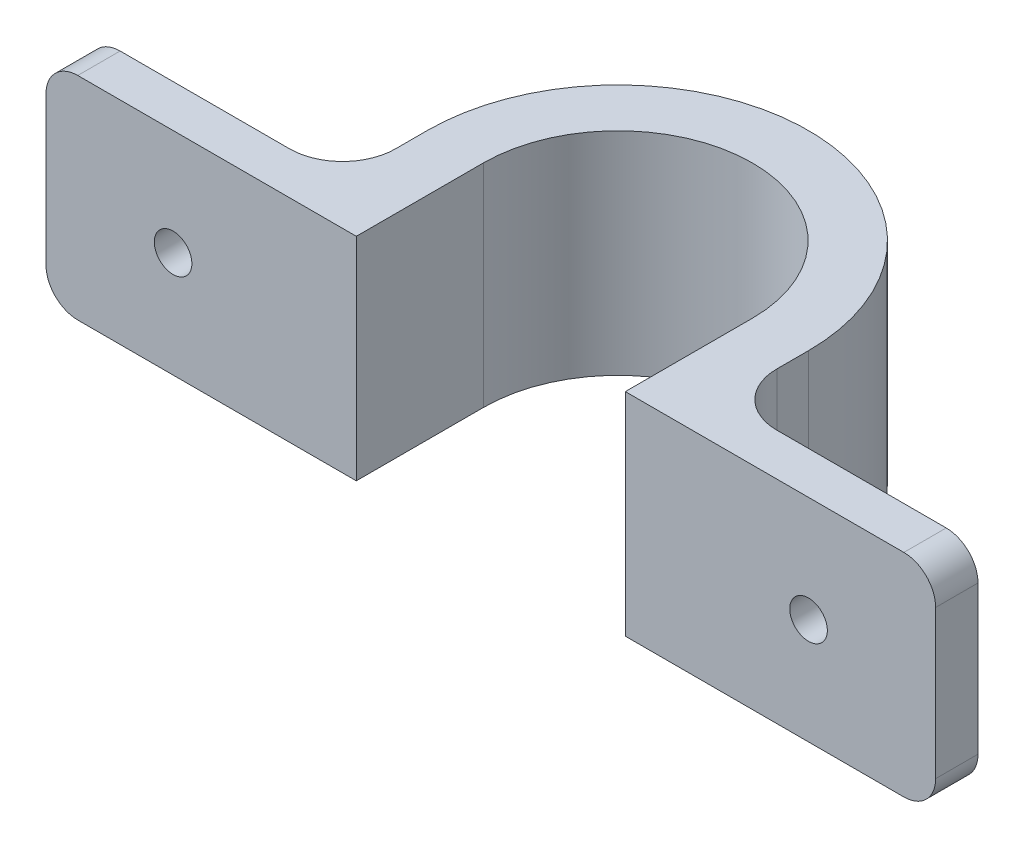
SolidWorks part; units mm, degrees
ref_plane "Front Plane" through (0, 0, 0) normal (0, 0, 1) x (1, 0, 0)
ref_plane "Top Plane" through (0, 0, 0) normal (0, 1, 0) x (1, 0, 0)
ref_plane "Right Plane" through (0, 0, 0) normal (1, 0, 0) x (0, 0, -1)
sketch "Sketch1" plane through (0, 0, 0) normal (0, 1, 0) x (1, 0, 0)
  line L0 (0, 0) -> (0, 4)
  line L1 (0, 4) -> (24, 4)
  line L2 (60, 4) -> (84, 4)
  line L3 (84, 4) -> (84, 0)
  line L6 (29.3, 12) -> (29.3, 0)
  line L7 (29.3, 0) -> (0, 0)
  line L8 (54.7, 12) -> (54.7, 0)
  line L9 (54.7, 0) -> (84, 0)
  line L10 (29.3, 12) -> (54.7, 12) construction
  line L11 (24, 12) -> (24, 4)
  line L12 (60, 12) -> (60, 4)
  line L13 (12, 4) -> (12, 0) construction
  line L14 (72, 4) -> (72, 0) construction
  arc A1 (54.7, 12) -> (29.3, 12) centre (42, 12) ccw
  arc A2 (60, 12) -> (24, 12) centre (42, 12) ccw
  dimension "D3" = 12
  dimension "D4" = 18
  dimension "D1" = 12.7
  dimension "D2" = 4
  dimension "D5" = 60
extrude "Boss-Extrude1" add sketch "Sketch1" along normal blind 20
sketch "Sketch2" plane through (0, 0, -4) normal (0, 0, -1) x (-1, 0, 0)
  line L0 (-42, 20) -> (-42, 0) construction
  line L1 (-24, 20) -> (-60, 20) construction
  line L2 (-60, 0) -> (-24, 0) construction
  line L3 (-72, 10) -> (-42, 10) construction
  line L4 (-42, 10) -> (-12, 10) construction
  circle A1 centre (-72, 10) radius 1.775
  circle A2 centre (-12, 10) radius 1.775
  dimension "D1" = 3.55
  dimension "D2" = 60
extrude "Cut-Extrude1" cut sketch "Sketch2" against normal through all
fillet "Fillet1" radius 3 4 edges at (0, 0, -2) (0, 20, -2) (84, 0, -2) (84, 20, -2)
fillet "Fillet2" radius 5 2 edges at (60, 10, -4) (24, 10, -4)
